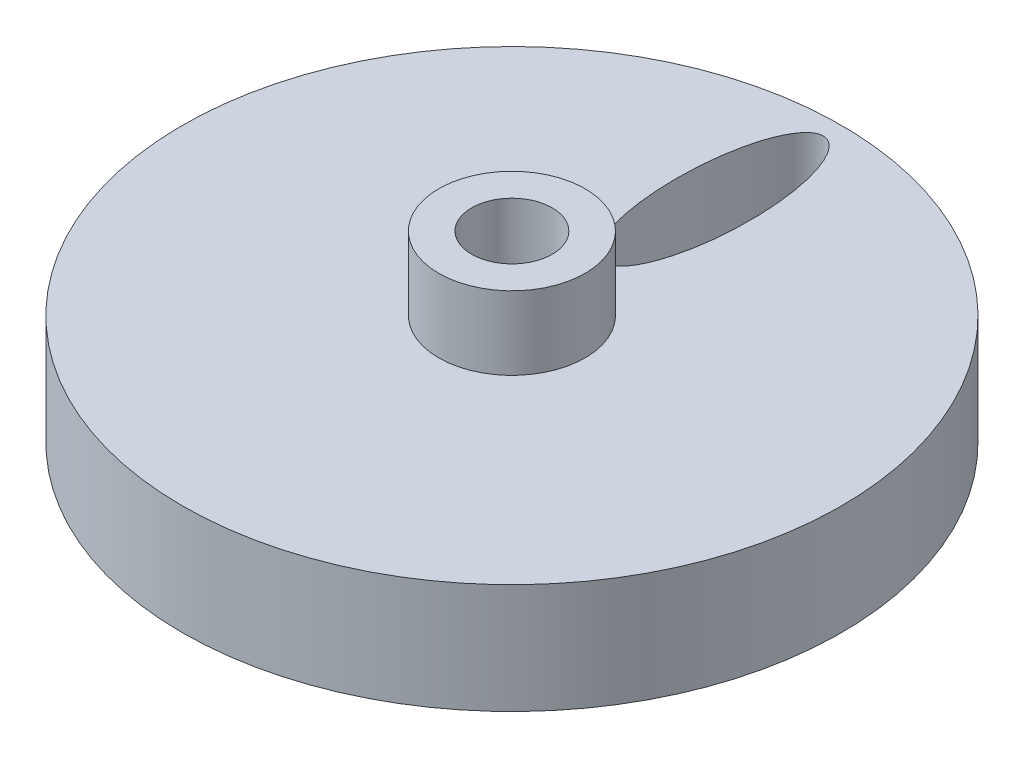
SolidWorks part; units mm, degrees
ref_plane "Front Plane" through (0, 0, 0) normal (0, 0, 1) x (1, 0, 0)
ref_plane "Top Plane" through (0, 0, 0) normal (0, 1, 0) x (1, 0, 0)
ref_plane "Right Plane" through (0, 0, 0) normal (1, 0, 0) x (0, 0, -1)
sketch "Sketch1" plane through (0, 0, 0) normal (0, 1, 0) x (1, 0, 0)
  circle A0 centre (0, 0) radius 9
  dimension "D1" = 18
extrude "Boss-Extrude1" add sketch "Sketch1" along normal blind 3
sketch "Sketch2" plane through (0, 3, 0) normal (0, 1, 0) x (1, 0, 0)
  circle A0 centre (0, 0) radius 2
  dimension "D1" = 4
extrude "Boss-Extrude2" add sketch "Sketch2" along normal blind 2
sketch "Sketch3" plane through (0, 5, 0) normal (0, 1, 0) x (1, 0, 0)
  circle A0 centre (0, 0) radius 1.1
  dimension "D1" = 2.2
extrude "Cut-Extrude1" cut sketch "Sketch3" against normal blind 2
sketch "Sketch4" plane through (0, 3, 0) normal (0, 1, 0) x (1, 0, 0)
  line L0 (0, 0) -> (0, 9) construction
  circle A0 centre (0, 0) radius 9 construction
  circle A1 centre (0, 0) radius 2 construction
  ellipse E0 centre (0, 5.4993) end of major axis (0, 8.4993) minor radius 1
  dimension "D3" = 0.5007
  dimension "D1" = 2
  dimension "D2" = 6
  dimension "D4" = 2.4993
extrude "Cut-Extrude2" cut sketch "Sketch4" against normal blind 3
